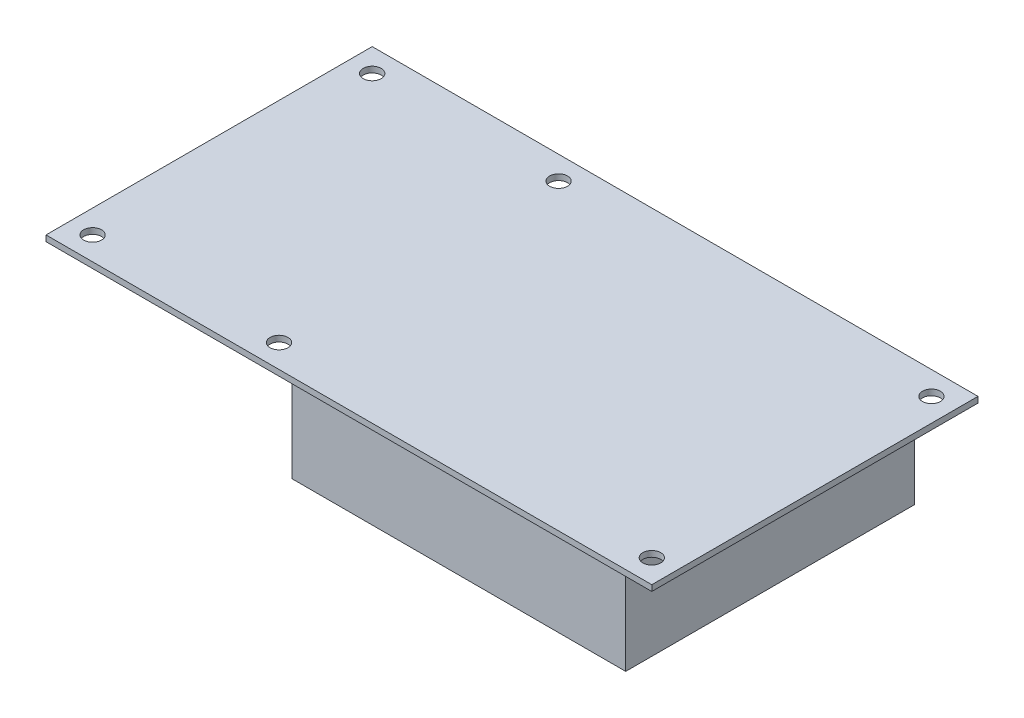
SolidWorks part; units mm, degrees
ref_plane "Front Plane" through (0, 0, 0) normal (0, 0, 1) x (1, 0, 0)
ref_plane "Top Plane" through (0, 0, 0) normal (0, 1, 0) x (1, 0, 0)
ref_plane "Right Plane" through (0, 0, 0) normal (1, 0, 0) x (0, 0, -1)
sketch "Sketch1" plane through (0, 0, 0) normal (0, 1, 0) x (1, 0, 0)
  line L1 (0, 0) -> (165.1, 0)
  line L2 (0, 0) -> (0, 88.9)
  line L3 (0, 88.9) -> (165.1, 88.9)
  line L4 (165.1, 0) -> (165.1, 88.9)
  dimension "D1" = 165.1
  dimension "D2" = 88.9
extrude "Extrude1" add sketch "Sketch1" along normal blind 1.6002
sketch "Sketch2" plane through (0, 1.6002, 0) normal (0, 1, 0) x (-1, 0, 0)
  line L0 (-165.1, 0) -> (-165.1, -88.9) construction
  line L1 (0, 0) -> (-165.1, 0) construction
  circle A0 centre (-158.75, -6.35) radius 2.4384
  circle A1 centre (-57.15, -6.35) radius 2.4384
  circle A2 centre (-6.35, -6.35) radius 2.4384
  circle A3 centre (-158.75, -82.55) radius 2.4384
  circle A4 centre (-57.15, -82.55) radius 2.4384
  circle A5 centre (-6.35, -82.55) radius 2.4384
  dimension "D1" = 4.8768
  dimension "D2" = 4.8768
  dimension "D3" = 4.8768
  dimension "D4" = 4.8768
  dimension "D5" = 4.8768
  dimension "D6" = 4.8768
  dimension "D7" = 6.35
  dimension "D8" = 6.35
  dimension "D9" = 76.2
  dimension "D10" = 101.6
  dimension "D11" = 50.8
extrude "Cut-Extrude1" cut sketch "Sketch2" against normal through all
sketch "Sketch3" plane through (0, 0, 0) normal (0, -1, 0) x (1, 0, 0)
  line L0 (165.1, 0) -> (165.1, -88.9) construction
  line L1 (62.484, -4.572) -> (153.416, -4.572)
  line L2 (62.484, -4.572) -> (62.484, -83.312)
  line L3 (62.484, -83.312) -> (153.416, -83.312)
  line L4 (153.416, -4.572) -> (153.416, -83.312)
  line L5 (0, 0) -> (165.1, 0) construction
  line L6 (165.1, -88.9) -> (0, -88.9) construction
  dimension "D1" = 11.684
  dimension "D2" = 4.572
  dimension "D3" = 5.588
  dimension "D4" = 102.616
extrude "Extrude2" add sketch "Sketch3" along normal blind 27.0002
